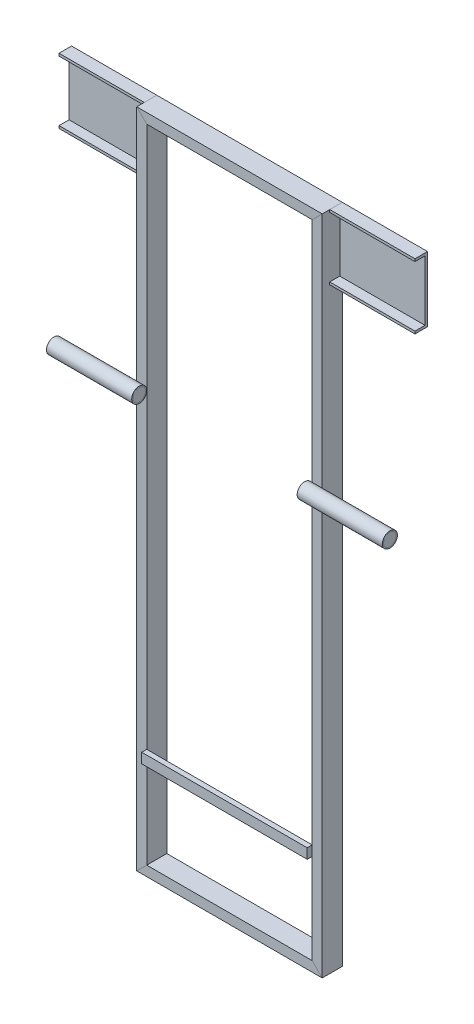
SolidWorks part; units mm, degrees
ref_plane "Front Plane" through (0, 0, 0) normal (0, 0, 1) x (1, 0, 0)
ref_plane "Top Plane" through (0, 0, 0) normal (0, 1, 0) x (1, 0, 0)
ref_plane "Right Plane" through (0, 0, 0) normal (1, 0, 0) x (0, 0, -1)
sketch "Sketch1" plane through (0, 0, 0) normal (0, 0, 1) x (1, 0, 0)
  line L0 (0, 0) -> (0, 1300)
  line L1 (0, 1300) -> (350, 1300)
  line L2 (350, 1300) -> (350, 0)
  line L3 (350, 0) -> (0, 0)
  dimension "D1" = 350
  dimension "D2" = 1300
other "Rectangular tube 50 X 30 X 2.6(1)"
ref_plane "Plane1" through (0, 0, -20) normal (0, 1, 0) x (-1, 0, 0)
sketch "Sketch11" plane through (0, 0, -20) normal (0, 1, 0) x (-1, 0, 0)
  line L0 (-4.8, -17.4) -> (4.8, -17.4)
  line L1 (-7.4, -14.8) -> (-7.4, 14.8)
  line L2 (4.8, 17.4) -> (-4.8, 17.4)
  line L3 (7.4, 14.8) -> (7.4, -14.8)
  line L4 (-4.8, -20) -> (4.8, -20)
  line L5 (-10, -14.8) -> (-10, 14.8)
  line L6 (4.8, 20) -> (-4.8, 20)
  line L7 (10, 14.8) -> (10, -14.8)
  line L8 (-10, 14.8) -> (-10, 20)
  line L9 (-10, 20) -> (-4.8, 20)
  line L10 (-7.4, 14.8) -> (-7.4, 17.4)
  line L11 (-7.4, 17.4) -> (-4.8, 17.4)
  line L12 (7.4, 14.8) -> (7.4, 17.4)
  line L13 (7.4, 17.4) -> (4.8, 17.4)
  line L14 (10, 14.8) -> (10, 20)
  line L15 (10, 20) -> (4.8, 20)
  line L16 (-7.4, -14.8) -> (-7.4, -17.4)
  line L17 (7.4, -14.8) -> (7.4, -17.4)
  line L18 (7.4, -17.4) -> (4.8, -17.4)
  line L19 (4.8, -20) -> (10, -20)
  line L20 (10, -20) -> (10, -14.8)
  line L21 (-4.8, -20) -> (-10, -20)
  line L22 (-10, -20) -> (-10, -14.8)
  line L23 (-7.4, -17.4) -> (-4.8, -17.4)
  point P0 (0, 20)
  point P1 (10, 0)
  point P2 (0, -20)
  point P3 (-10, 0)
  point P4 (-10, 20)
  point P5 (10, 20)
  point P6 (10, -20)
  point P7 (-10, -20)
  point P8 (0, 0)
  point P33 (0, 0)
  dimension "Thickness" = 2.6
  dimension "V_leg" = 40
  dimension "H_leg" = 20
other "Rectangular tube 50 X 30 X 2.6(4)"
ref_plane "Plane2" through (0, 1300, -20) normal (1, 0, 0) x (0, 1, 0)
sketch "Sketch12" plane through (0, 1300, -20) normal (1, 0, 0) x (0, 1, 0)
  line L0 (-4.8, -17.4) -> (4.8, -17.4)
  line L1 (-7.4, -14.8) -> (-7.4, 14.8)
  line L2 (4.8, 17.4) -> (-4.8, 17.4)
  line L3 (7.4, 14.8) -> (7.4, -14.8)
  line L4 (-4.8, -20) -> (4.8, -20)
  line L5 (-10, -14.8) -> (-10, 14.8)
  line L6 (4.8, 20) -> (-4.8, 20)
  line L7 (10, 14.8) -> (10, -14.8)
  line L8 (-7.4, 14.8) -> (-7.4, 17.4)
  line L9 (-6.6875, 17.4) -> (-4.8, 17.4)
  line L10 (-10, 14.8) -> (-10, 20)
  line L11 (-10, 20) -> (-4.8, 20)
  line L12 (4.8, 20) -> (10, 20)
  line L13 (10, 20) -> (10, 14.8)
  line L14 (7.4, 14.8) -> (7.4, 17.4)
  line L15 (7.4, 17.4) -> (4.8, 17.4)
  line L16 (4.8, -17.4) -> (7.4, -17.4)
  line L17 (7.4, -17.4) -> (7.4, -14.8)
  line L18 (10, -14.8) -> (10, -20)
  line L19 (10, -20) -> (4.8, -20)
  line L20 (-4.8, -20) -> (-10, -20)
  line L21 (-10, -20) -> (-10, -14.8)
  line L22 (-7.4, 17.4) -> (-6.6875, 17.4)
  line L23 (-7.4, -14.8) -> (-7.4, -17.4)
  line L24 (-7.4, -17.4) -> (-4.8, -17.4)
  point P0 (0, 20)
  point P1 (10, 0)
  point P2 (0, -20)
  point P3 (-10, 0)
  point P4 (-10, 20)
  point P5 (10, 20)
  point P6 (10, -20)
  point P7 (-10, -20)
  point P8 (0, 0)
  point P33 (0, 0)
  dimension "Thickness" = 2.6
  dimension "V_leg" = 40
  dimension "H_leg" = 20
other "Trim/Extend1"
other "Trim/Extend2"
other "Trim/Extend4"
other "Trim/Extend5"
sketch "Sketch14" plane through (0, 0, 0) normal (0, 0, 1) x (1, 0, 0)
  line L0 (350, 0) -> (0, 0) construction
  line L1 (10, 210) -> (340, 210)
  line L2 (10, 210) -> (10, 190)
  line L3 (10, 190) -> (340, 190)
  line L4 (340, 210) -> (340, 190)
  point P6 (175, 190)
  point P7 (175, 0)
  dimension "D1" = 330
  dimension "D2" = 20
  dimension "D3" = 210
extrude "Boss-Extrude1" add sketch "Sketch14" along normal blind 10 separate body
sketch "Sketch19" plane through (0, 0, -40) normal (0, 0, -1) x (-1, 0, 0)
  line L0 (-360, 1310) -> (-530, 1310)
  line L1 (10, 1310) -> (180, 1310)
  dimension "D1" = 170
other "C channel 120 X 12(5)"
ref_plane "Plane3" through (-10, 1180, -40) normal (-1, 0, 0) x (0, 0, 1)
sketch "Sketch111" plane through (-10, 1180, -40) normal (-1, 0, 0) x (0, 0, 1)
  line L0 (25, 130) -> (0, 130)
  line L1 (25, 0) -> (0, 0)
  line L2 (0, 130) -> (0, 0)
  line L3 (25, 125) -> (25, 130)
  line L4 (25, 125) -> (13.4638, 125)
  line L5 (5, 125) -> (5, 101.74)
  line L7 (25, 5) -> (25, 0)
  line L8 (5, 125) -> (13.4638, 125)
  line L9 (5, 18.27) -> (5, 5)
  line L10 (5, 5) -> (25, 5)
  line L12 (5, 101.74) -> (5, 18.27)
  point P8 (0, 65)
  point P9 (5, 60.005)
  point P10 (12.5, 130)
  point P11 (12.5, 0)
  point P12 (25, 9.1013)
  point P13 (25, 110.9087)
  point P14 (0, 0)
  dimension "Depth" = 130
  dimension "BF" = 25
  dimension "TW" = 5
sketch "Sketch112" plane through (0, 0, 0) normal (0, 0, 1) x (1, 0, 0)
  line L0 (340, 830) -> (510, 830)
  line L1 (10, 830) -> (-160, 830)
  line L3 (0, 1300) -> (350, 1300) construction
  line L5 (10, 1290) -> (10, 10) construction
  line L6 (340, 1290) -> (340, 10) construction
  dimension "D1" = 170
  dimension "D2" = 470
  dimension "D3" = 470
other "Pipe 21.3 X 2.3(1)"
ref_plane "Plane4" through (340, 830, 15) normal (1, 0, 0) x (0, 1, 0)
sketch "Sketch114" plane through (340, 830, 15) normal (1, 0, 0) x (0, 1, 0)
  circle A0 centre (0, 0) radius 12.5
  circle A1 centre (0, 0) radius 15
  point P3 (0, 0)
  point P5 (15, 0)
  point P6 (0, -15)
  dimension "In_dia" = 25
  dimension "Out_dia" = 30
surface "Surface-Plane1"
surface "Surface-Plane2"
surface "Surface-Plane3"
